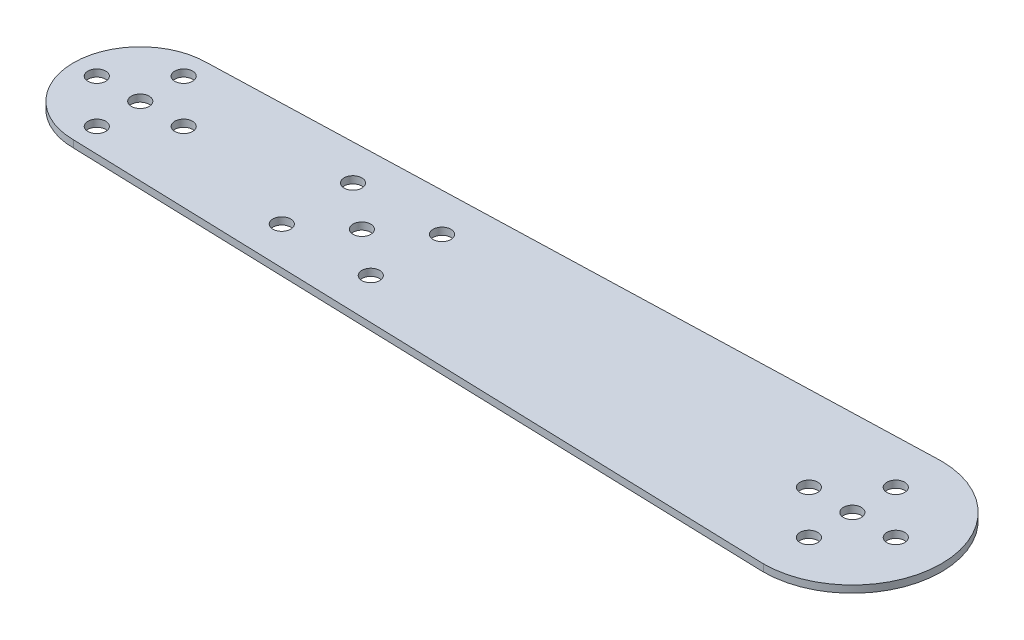
SolidWorks part; units mm, degrees
ref_plane "Front Plane" through (0, 0, 0) normal (0, 0, 1) x (1, 0, 0)
ref_plane "Top Plane" through (0, 0, 0) normal (0, 1, 0) x (1, 0, 0)
ref_plane "Right Plane" through (0, 0, 0) normal (1, 0, 0) x (0, 0, -1)
sketch "Sketch2" plane through (0, 0, 0) normal (0, 1, 0) x (1, 0, 0)
  line L0 (-155.0973, 0) -> (170.648, 0) construction
  line L1 (0, 82.4594) -> (0, -74.2748) construction
  line L2 (100, -40.9921) -> (100, 25) construction
  line L3 (-100, 48.0857) -> (-100, -40.9921) construction
  line L4 (100, 25) -> (-100, 18.75)
  line L5 (100, -25) -> (-100, -18.75)
  arc A2 (100, -25) -> (100, 25) centre (100, 0) ccw
  arc A3 (-100, 18.75) -> (-100, -18.75) centre (-100, 0) ccw
  point P3 (100, 0)
  point P6 (-100, 0)
  point P15 (100, -25)
  point P16 (100, 25)
  point P17 (-100, -18.75)
  point P19 (-100, 18.75)
  dimension "D3" = 50
  dimension "D4" = 37.5
  dimension "D1" = 100
  dimension "D2" = 100
extrude "Boss-Extrude1" add sketch "Sketch2" along normal blind 2
sketch "Sketch4" plane through (0, 2, 0) normal (0, 1, 0) x (1, 0, 0)
  line L0 (-123.9495, 0) -> (119.0142, 0) construction
  line L1 (0, 42.9025) -> (0, -31.7629) construction
  line L2 (100, 42.9025) -> (100, -35.5101) construction
  line L3 (-100, 42.9025) -> (-100, -35.5101) construction
  circle A0 centre (100, 12.2) radius 2.5
  circle A1 centre (100, -12.2) radius 2.5
  circle A2 centre (112.2, 0) radius 2.5
  circle A3 centre (87.8, 0) radius 2.5
  circle A4 centre (-100, 12.2) radius 2.5
  circle A5 centre (-87.8, 0) radius 2.5
  circle A6 centre (-112.2, 0) radius 2.5
  circle A7 centre (-100, -12.2) radius 2.5
  point P9 (100, 12.2)
  point P10 (100, 0)
  point P11 (112.2, 0)
  point P12 (-100, 0)
  point P13 (-100, 12.2)
  point P14 (100, -12.2)
  point P15 (87.8, 0)
  point P20 (100, 0)
  point P24 (-87.8, 0)
  point P25 (-100, -12.2)
  point P26 (-112.2, 0)
  point P31 (-100, 0)
  dimension "D1" = 100
  dimension "D6" = 5
  dimension "D7" = 5
  dimension "D8" = 5
  dimension "D9" = 5
  dimension "D10" = 5
  dimension "D11" = 5
  dimension "D12" = 5
  dimension "D13" = 5
  dimension "D2" = 12.2
  dimension "D4" = 12.2
  dimension "D14" = 100
  dimension "D15" = 100
  dimension "D3" = 4
  dimension "D5" = 4
hole_wizard "Ø5.0mm Dowel Hole1" positions "Sketch9" profile "Sketch10" hole size "Ø5.0" standard "ANSI Metric" end condition up to next
sketch "Sketch9" plane through (0, 2, 0) normal (0, 1, 0) x (1, 0, 0)
  point P0 (100, 0)
  point P3 (-100, 0)
sketch "Sketch10" plane through (100, 2, 0) normal (1, 0, 0) x (0, 0, 1)
  line L0 (0, 0) -> (0, 2)
  line L1 (0, 2) -> (2.5, 2)
  line L2 (2.5, 2) -> (2.5, 0)
  line L5 (2.5, 0) -> (0, 0)
  line L11 (0, -6.35) -> (0, 107.95) construction
  dimension "Thru Hole Dia." = 5
  dimension "Thru Hole Depth" = 2
extrude "Cut-Extrude1" cut sketch "Sketch4" against normal up to next
sketch "Sketch11" plane through (0, 2, 0) normal (0, 1, 0) x (1, 0, 0)
  line L0 (0, 40.9767) -> (0, -46.3977) construction
  line L1 (-109.4412, 0) -> (117.2856, 0) construction
  point P6 (-50, 0)
  point P7 (50, 0)
  dimension "D1" = 50
sketch "Sketch16" plane through (0, 2, 0) normal (0, 1, 0) x (1, 0, 0)
  circle A2 centre (-37.75, 0) radius 2.5
  circle A3 centre (-25.25, 10) radius 2.5
  circle A4 centre (-25.25, -10) radius 2.5
  circle A5 centre (-50.25, 10) radius 2.5
  circle A6 centre (-50.25, -10) radius 2.5
extrude "Cut-Extrude2" cut sketch "Sketch16" against normal up to next
equation "\"Length\"= 200"
equation "\"Width\"= 50"
equation "\"D1@Sketch2\"=\"Length\"/2"
equation "\"D2@Sketch2\"=\"Length\"/2"
equation "\"D4@Sketch2\"=\"Width\"*0.75"
equation "\"thick\"=2"
equation "\"D1@Boss-Extrude1\"=\"thick\""
equation "\"D3@Sketch2\"=\"Width\""
equation "\"D1@Sketch4\"=\"Length\"/2"
equation "\"External_HoleDIa\"=5"
equation "\"D13@Sketch4\"=\"External_HoleDIa\""
equation "\"D12@Sketch4\"=\"External_HoleDIa\""
equation "\"D10@Sketch4\"=\"External_HoleDIa\""
equation "\"D11@Sketch4\"=\"External_HoleDIa\""
equation "\"D7@Sketch4\"=\"External_HoleDIa\""
equation "\"D8@Sketch4\"=\"External_HoleDIa\""
equation "\"D9@Sketch4\"=\"External_HoleDIa\""
equation "\"D6@Sketch4\"=\"External_HoleDIa\""
equation "\"D1@Sketch11\"=\"Length\"/4"
equation "\"D14@Sketch4\"=\"Length\"/2"
equation "\"D15@Sketch4\"=\"Length\"/2"
